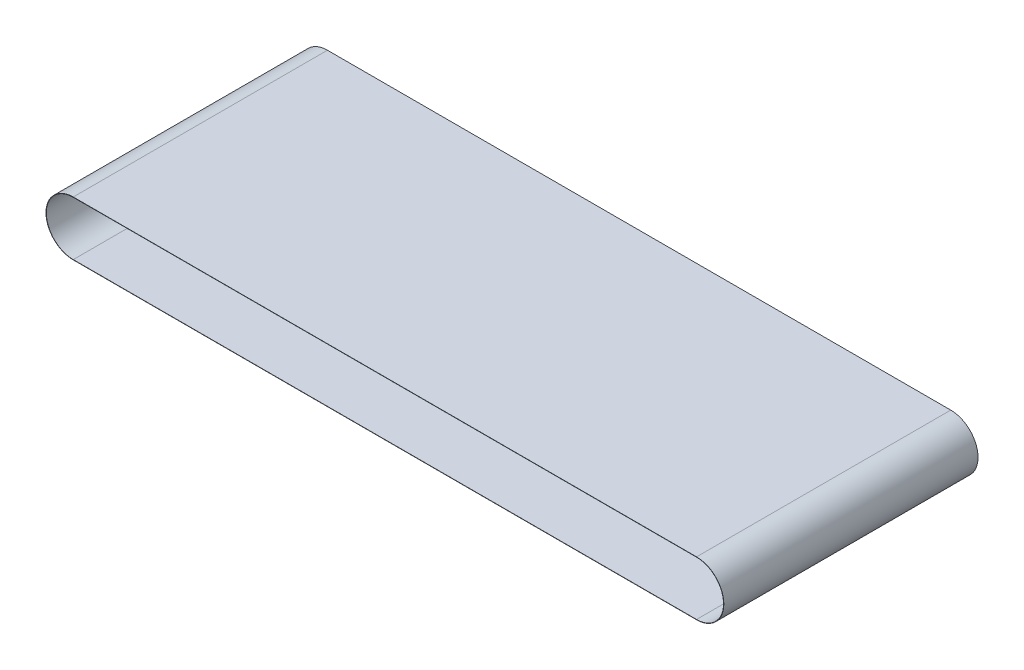
SolidWorks part; units mm, degrees
material "Silicon Rubber"
ref_plane "Front Plane" through (0, 0, 0) normal (0, 0, 1) x (1, 0, 0)
ref_plane "Top Plane" through (0, 0, 0) normal (0, 1, 0) x (1, 0, 0)
ref_plane "Right Plane" through (0, 0, 0) normal (1, 0, 0) x (0, 0, -1)
sketch "Sketch1" plane through (0, 0, 0) normal (0, 0, 1) x (1, 0, 0)
  line L0 (0, 24.511) -> (560.578, 24.511)
  line L1 (0, -24.511) -> (560.578, -24.511)
  line L2 (0, 24.257) -> (560.578, 24.257)
  line L3 (0, -24.257) -> (560.578, -24.257)
  arc A0 (0, 24.511) -> (0, -24.511) centre (0, 0) ccw
  arc A1 (560.578, -24.511) -> (560.578, 24.511) centre (560.578, 0) ccw
  arc A2 (560.578, -24.257) -> (560.578, 24.257) centre (560.578, 0) ccw
  arc A3 (0, 24.257) -> (0, -24.257) centre (0, 0) ccw
  point P1 (-24.511, 0)
  point P4 (585.089, 0)
  dimension "D1" = 24.511
  dimension "D2" = 609.6
  dimension "D3" = 0.254
extrude "Boss-Extrude1" add sketch "Sketch1" against normal mid plane 228.6
